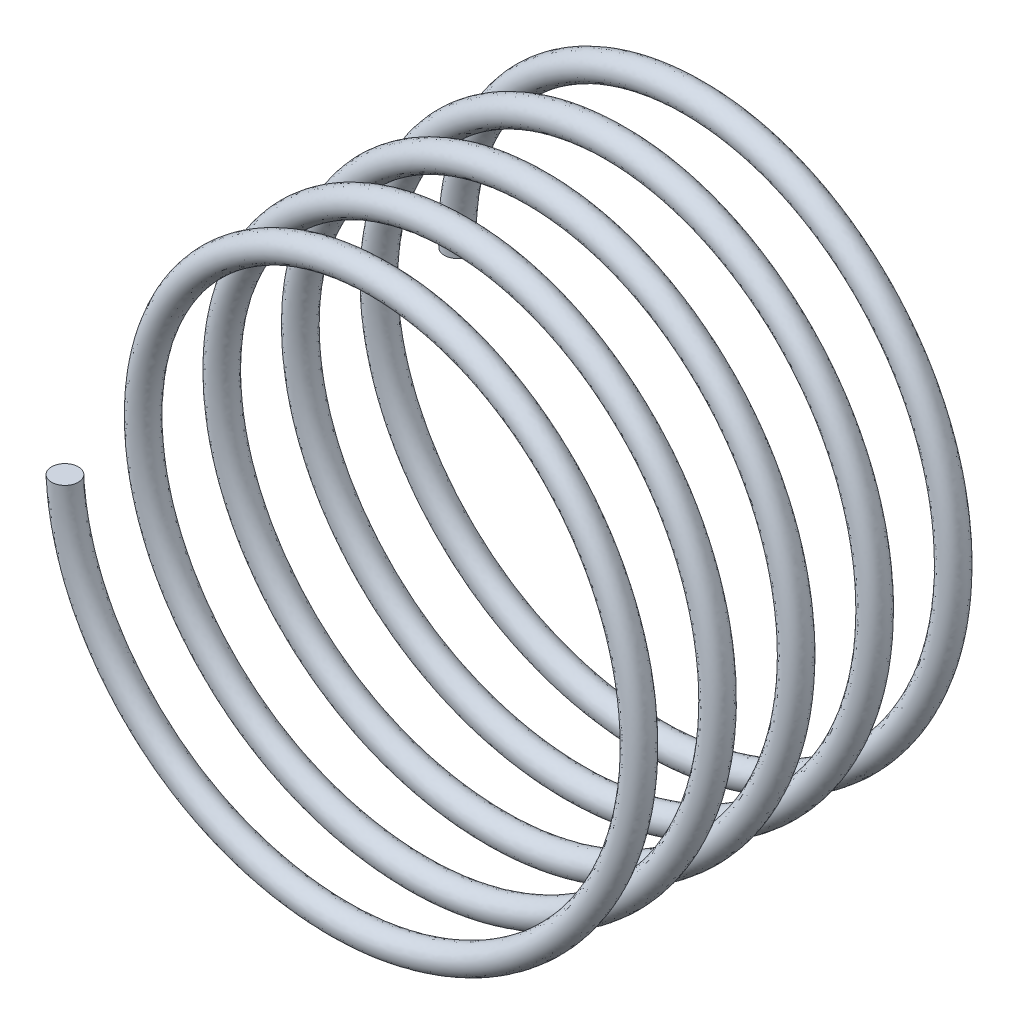
SolidWorks part; units mm, degrees
ref_plane "Front Plane" through (0, 0, 0) normal (0, 0, 1) x (1, 0, 0)
ref_plane "Top Plane" through (0, 0, 0) normal (0, 1, 0) x (1, 0, 0)
ref_plane "Right Plane" through (0, 0, 0) normal (1, 0, 0) x (0, 0, -1)
sketch "Sketch1" plane through (0, 0, 0) normal (0, 0, 1) x (1, 0, 0)
  circle A0 centre (0, 0) radius 5.08
curve "Helix/Spiral1" pitch 1.492 height 7.46 turns 5
sketch "Sketch4" plane through (0, 0, 0) normal (0, 1, 0) x (1, 0, 0)
  circle A0 centre (-5.0756, -7.465) radius 0.254
  point P2 (-5.321, -7.4312)
  point P3 (-5.7677, -6.6334)
  point P4 (-5.0756, -7.465)
sketch "Sketch7" plane through (0, 0, 0) normal (1, 0, 0) x (0, 0, -1)
  line L0 (-7.8437, 0.7778) -> (-9.2098, 0.7778)
  line L1 (0, -0.762) -> (1.3173, -0.762)
  arc A0 (-7.0817, 0.0158) -> (-7.8437, 0.7778) centre (-7.8437, 0.0158) ccw
  arc A1 (-0.762, 0) -> (0, -0.762) centre (0, 0) ccw
sweep "Sweep1" add profiles "Sketch4" path "Helix/Spiral1"
